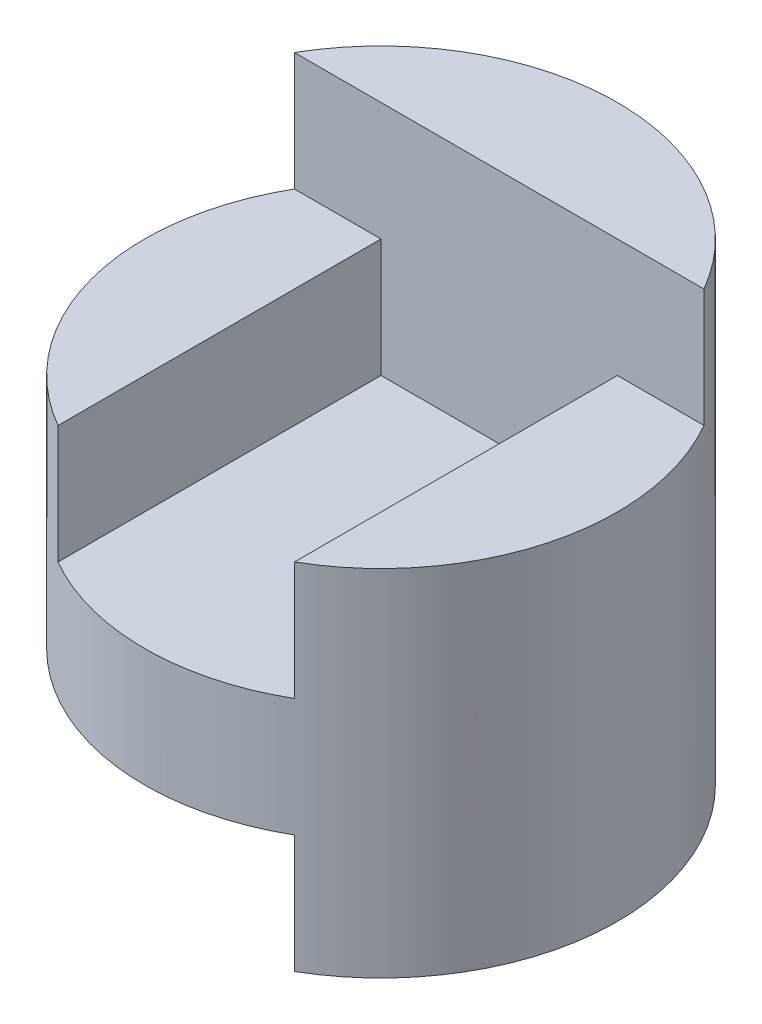
SolidWorks part; units mm, degrees
ref_plane "Front" through (0, 0, 0) normal (0, 0, 1) x (1, 0, 0)
ref_plane "Top" through (0, 0, 0) normal (0, 1, 0) x (1, 0, 0)
ref_plane "Right" through (0, 0, 0) normal (1, 0, 0) x (0, 0, -1)
sketch "Sketch1" plane through (0, 0, 0) normal (0, 1, 0) x (1, 0, 0)
  circle A0 centre (0, 0) radius 2
  dimension "D1" = 4
extrude "Boss-Extrude1" add sketch "Sketch1" along normal blind 4
sketch "Sketch2" plane through (0, 0, 0) normal (0, 0, 1) x (1, 0, 0)
  line L0 (-2, 4) -> (2, 4)
  line L1 (2, 4) -> (2, 3)
  line L2 (2, 0) -> (2, 4) construction
  line L3 (2, 3) -> (1, 3)
  line L4 (1, 3) -> (1, 2)
  line L5 (1, 2) -> (-1, 2)
  line L6 (-1, 2) -> (-1, 3)
  line L7 (-1, 3) -> (-2, 3)
  line L8 (-2, 3) -> (-2, 4)
  dimension "D1" = 1
  dimension "D2" = 1
  dimension "D3" = 1
  dimension "D4" = 1
  dimension "D5" = 1
extrude "Cut-Extrude1" cut sketch "Sketch2" against normal blind 1 and the other way blind 3
sketch "Sketch4" plane through (0, 0, 0) normal (0, -1, 0) x (1, 0, 0)
  line L1 (-1, -1) -> (-1.7321, -1)
  line L2 (1, 1.7321) -> (1, -1)
  line L3 (1, -1) -> (-1, -1)
  arc A1 (-1.7321, -1) -> (1, 1.7321) centre (0, 0) cw
extrude "Cut-Extrude9" cut sketch "Sketch4" against normal blind 1
